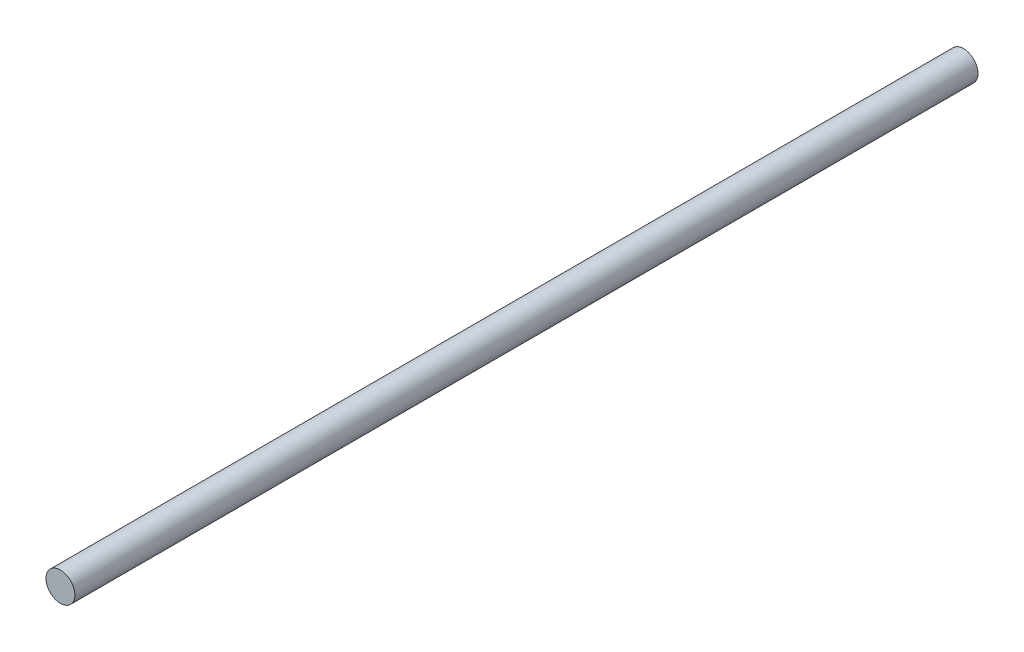
SolidWorks part; units mm, degrees
ref_plane "Front Plane" through (0, 0, 0) normal (0, 0, 1) x (1, 0, 0)
ref_plane "Top Plane" through (0, 0, 0) normal (0, 1, 0) x (1, 0, 0)
ref_plane "Right Plane" through (0, 0, 0) normal (1, 0, 0) x (0, 0, -1)
sketch "Sketch1" plane through (0, 0, 0) normal (0, 0, 1) x (1, 0, 0)
  circle A0 centre (0, 0) radius 4
  dimension "D1" = 8
extrude "Boss-Extrude1" add sketch "Sketch1" along normal blind 250
